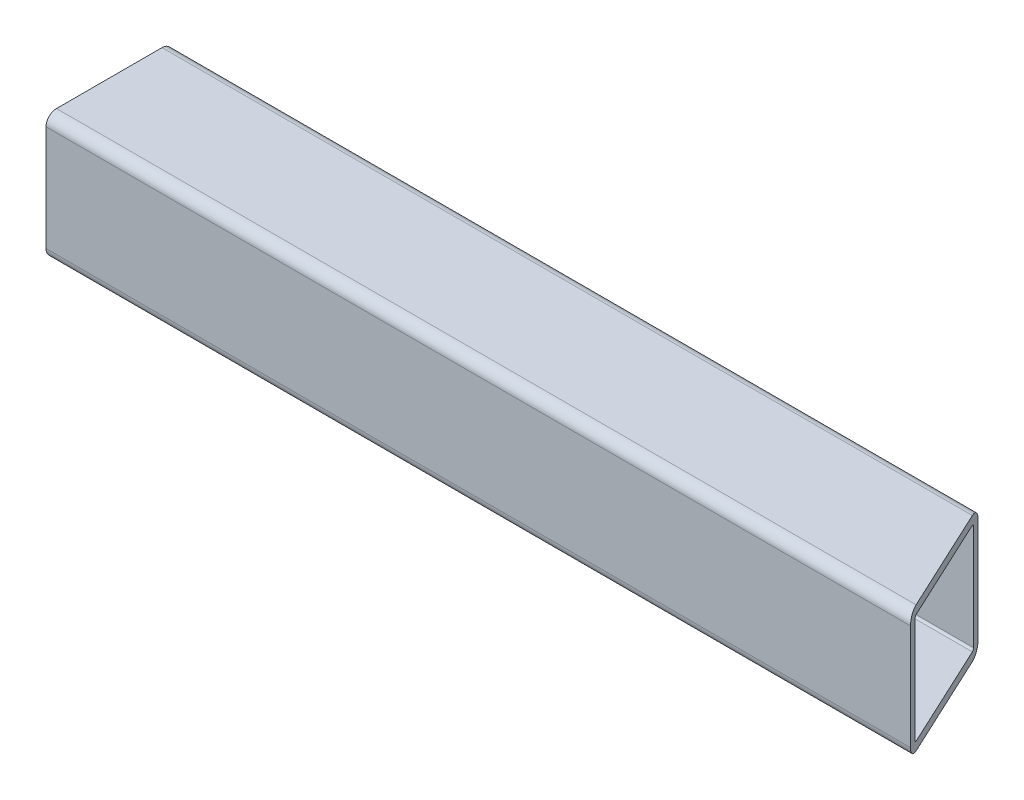
SolidWorks part; units mm, degrees
ref_plane "Front Plane" through (0, 0, 0) normal (0, 0, 1) x (1, 0, 0)
ref_plane "Top Plane" through (0, 0, 0) normal (0, 1, 0) x (1, 0, 0)
ref_plane "Right Plane" through (0, 0, 0) normal (1, 0, 0) x (0, 0, -1)
sketch "Sketch1" plane through (0, 0, 0) normal (1, 0, 0) x (0, 0, -1)
  line L1 (-15.875, 19.05) -> (15.875, 19.05)
  line L2 (-19.05, 15.875) -> (-19.05, -15.875)
  line L3 (-15.875, -19.05) -> (15.875, -19.05)
  line L4 (19.05, 15.875) -> (19.05, -15.875)
  line L5 (-19.05, 19.05) -> (19.05, -19.05) construction
  line L6 (-19.05, -19.05) -> (19.05, 19.05) construction
  arc A0 (-19.05, -15.875) -> (-15.875, -19.05) centre (-15.875, -15.875) ccw
  arc A1 (15.875, -19.05) -> (19.05, -15.875) centre (15.875, -15.875) ccw
  arc A2 (19.05, 15.875) -> (15.875, 19.05) centre (15.875, 15.875) ccw
  arc A3 (-15.875, 19.05) -> (-19.05, 15.875) centre (-15.875, 15.875) ccw
  point P0 (0, 0)
  dimension "D3" = 3.175
  dimension "D1" = 38.1
  dimension "D2" = 38.1
extrude "Extrude-Thin1" add sketch "Sketch1" along normal mid plane 260.35 thin
sketch "Sketch2" plane through (0, -19.05, 0) normal (0, -1, 0) x (1, 0, 0)
  line L0 (130.175, 0) -> (-130.175, 0) construction
  line L1 (130.175, 15.875) -> (130.175, -15.875) construction
  line L2 (-130.175, 15.875) -> (-130.175, -15.875) construction
  line L3 (79.375, 15.875) -> (79.375, -15.875) construction
  line L4 (130.175, 15.875) -> (-130.175, 15.875) construction
  line L5 (130.175, -15.875) -> (-130.175, -15.875) construction
  line L6 (-79.375, 15.875) -> (-79.375, -15.875) construction
  dimension "D1" = 209.55
  dimension "D2" = 50.8
sketch "Sketch3" plane through (0, 19.05, 0) normal (0, 1, 0) x (1, 0, 0)
  line L0 (130.175, -19.05) -> (112.4087, 19.05)
  line L1 (130.175, 19.05) -> (-130.175, 19.05) construction
  line L3 (130.175, 15.875) -> (130.175, -15.875) construction
  dimension "D1" = 25
extrude "Cut-Extrude1" cut sketch "Sketch3" against normal through all and the other way through all flip side to cut
sketch "Sketch4" plane through (-130.175, 0, 0) normal (-1, 0, 0) x (0, 0, 1)
  line L0 (0, 16.51) -> (0, -16.51) construction
  line L1 (-15.875, 16.51) -> (15.875, 16.51) construction
  line L2 (16.51, 0) -> (-16.51, 0) construction
  line L3 (16.51, 15.875) -> (16.51, -15.875) construction
  line L4 (-16.51, -15.875) -> (-16.51, 15.875) construction
  line L5 (15.875, -16.51) -> (-15.875, -16.51) construction
